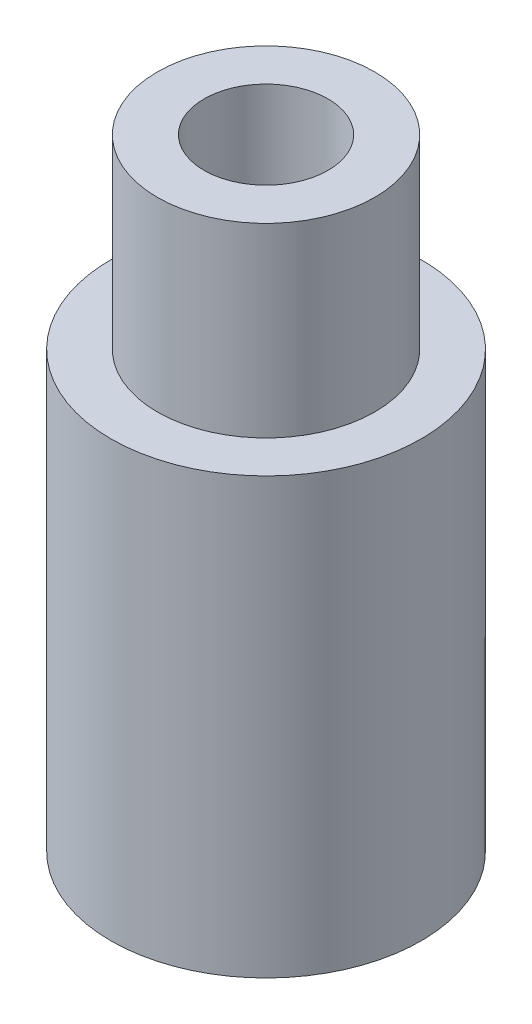
SolidWorks part; units mm, degrees
material "PVC 0.007 Plasticized"
ref_plane "Front Plane" through (0, 0, 0) normal (0, 0, 1) x (1, 0, 0)
ref_plane "Top Plane" through (0, 0, 0) normal (0, 1, 0) x (1, 0, 0)
ref_plane "Right Plane" through (0, 0, 0) normal (1, 0, 0) x (0, 0, -1)
other "Configuration Table"
sketch "Sketch1" plane through (0, 0, 0) normal (0, 1, 0) x (1, 0, 0)
  circle A0 centre (0, 0) radius 2.5019
  dimension "D1" = 5.0038
extrude "Boss-Extrude1" add sketch "Sketch1" along normal blind 7.0104
sketch "Sketch2" plane through (0, 7.0104, 0) normal (0, 1, 0) x (1, 0, 0)
  circle A0 centre (0, 0) radius 1.7526
  dimension "D1" = 3.5052
extrude "Boss-Extrude2" add sketch "Sketch2" along normal blind 2.9972
sketch "Sketch3" plane through (0, 10.0076, 0) normal (0, 1, 0) x (1, 0, 0)
  circle A0 centre (0, 0) radius 0.9995
  dimension "D1" = 1.999
extrude "Cut-Extrude1" cut sketch "Sketch3" against normal through all
sketch "Sketch4" plane through (0, 0, 0) normal (0, -1, 0) x (1, 0, 0)
  circle A0 centre (0, 0) radius 1.9939
  dimension "D1" = 3.9878
extrude "Cut-Extrude2" cut sketch "Sketch4" against normal blind 6.985
